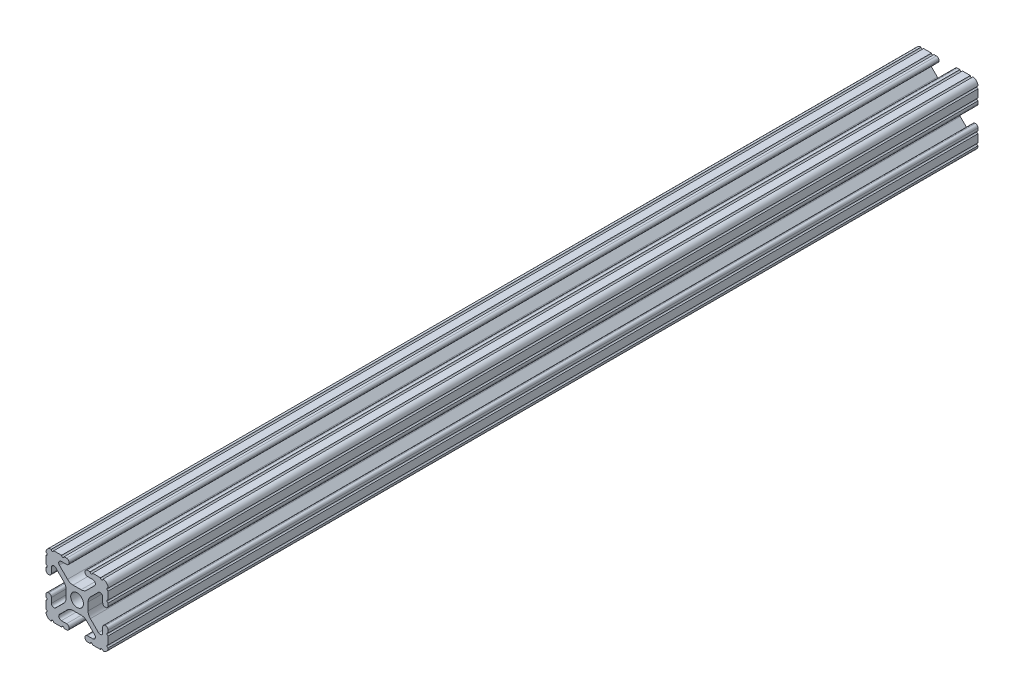
SolidWorks part; units mm, degrees
ref_plane "Front Plane" through (0, 0, 0) normal (0, 0, 1) x (1, 0, 0)
ref_plane "Top Plane" through (0, 0, 0) normal (0, 1, 0) x (1, 0, 0)
ref_plane "Right Plane" through (0, 0, 0) normal (1, 0, 0) x (0, 0, -1)
sketch "Sketch1" plane through (0, 0, 0) normal (0, 0, 1) x (1, 0, 0)
  line L88 (-7.1797, -8.6452) -> (-3.9523, -5.4237)
  line L89 (-1.7093, -4.4958) -> (1.7093, -4.4958)
  line L90 (3.9523, -5.4237) -> (7.1797, -8.6452)
  line L91 (6.4164, -10.4902) -> (4.2875, -10.4902)
  line L92 (3.2385, -11.5392) -> (3.2385, -11.651)
  line L93 (4.2875, -12.7) -> (5.3171, -12.7)
  line L94 (6.3331, -12.7) -> (9.5504, -12.7)
  line L95 (12.7, -9.5504) -> (12.7, -6.3331)
  line L96 (12.7, -5.3171) -> (12.7, -4.2875)
  line L97 (11.651, -3.2385) -> (11.5392, -3.2385)
  line L98 (10.4902, -4.2875) -> (10.4902, -6.4021)
  line L99 (8.7371, -7.1294) -> (5.441, -3.8408)
  line L100 (4.5085, -1.5932) -> (4.5085, 1.5932)
  line L101 (5.441, 3.8408) -> (8.7371, 7.1294)
  line L102 (10.4902, 6.4021) -> (10.4902, 4.2875)
  line L103 (11.5392, 3.2385) -> (11.651, 3.2385)
  line L104 (12.7, 4.2875) -> (12.7, 5.3171)
  line L105 (12.7, 6.3331) -> (12.7, 9.5504)
  line L106 (9.5504, 12.7) -> (6.3331, 12.7)
  line L107 (5.3171, 12.7) -> (4.2875, 12.7)
  line L108 (3.2385, 11.651) -> (3.2385, 11.5392)
  line L109 (4.2875, 10.4902) -> (6.4768, 10.4902)
  line L110 (7.207, 8.7244) -> (3.8983, 5.4232)
  line L111 (1.6558, 4.4958) -> (-1.6558, 4.4958)
  line L112 (-3.8983, 5.4232) -> (-7.207, 8.7244)
  line L113 (-6.4768, 10.4902) -> (-4.2875, 10.4902)
  line L114 (-3.2385, 11.5392) -> (-3.2385, 11.651)
  line L115 (-4.2875, 12.7) -> (-5.3171, 12.7)
  line L116 (-6.3331, 12.7) -> (-9.5504, 12.7)
  line L117 (-12.7, 9.5504) -> (-12.7, 6.3331)
  line L118 (-12.7, 5.3171) -> (-12.7, 4.2875)
  line L119 (-11.651, 3.2385) -> (-11.5392, 3.2385)
  line L120 (-10.4902, 4.2875) -> (-10.4902, 6.4021)
  line L121 (-8.7371, 7.1294) -> (-5.441, 3.8408)
  line L122 (-4.5085, 1.5932) -> (-4.5085, -1.5932)
  line L123 (-5.441, -3.8408) -> (-8.7371, -7.1294)
  line L124 (-10.4902, -6.4021) -> (-10.4902, -4.2875)
  line L125 (-11.5392, -3.2385) -> (-11.651, -3.2385)
  line L126 (-12.7, -4.2875) -> (-12.7, -5.3171)
  line L127 (-12.7, -6.3331) -> (-12.7, -9.5504)
  line L128 (-9.5504, -12.7) -> (-6.3331, -12.7)
  line L129 (-5.3171, -12.7) -> (-4.2875, -12.7)
  line L130 (-3.2385, -11.651) -> (-3.2385, -11.5392)
  line L131 (-4.2875, -10.4902) -> (-6.4164, -10.4902)
  circle A1 centre (0, 0) radius 2.6035
  arc A104 (-7.1797, -8.6452) -> (-6.4164, -10.4902) centre (-6.4164, -9.4098) ccw
  arc A105 (-1.7093, -4.4958) -> (-3.9523, -5.4237) centre (-1.7093, -7.6708) ccw
  arc A106 (3.9523, -5.4237) -> (1.7093, -4.4958) centre (1.7093, -7.6708) ccw
  arc A107 (6.4164, -10.4902) -> (7.1797, -8.6452) centre (6.4164, -9.4098) ccw
  arc A108 (4.2875, -10.4902) -> (3.2385, -11.5392) centre (4.2875, -11.5392) ccw
  arc A109 (3.2385, -11.651) -> (4.2875, -12.7) centre (4.2875, -11.651) ccw
  arc A110 (6.3331, -12.7) -> (5.3171, -12.7) centre (5.8251, -12.7) ccw
  arc A111 (10.5664, -12.6998) -> (9.5504, -12.7) centre (10.0584, -12.7) ccw
  arc A112 (10.5664, -12.6998) -> (12.6998, -10.5664) centre (10.5918, -10.5918) ccw
  arc A113 (12.7, -9.5504) -> (12.6998, -10.5664) centre (12.7, -10.0584) ccw
  arc A114 (12.7, -5.3171) -> (12.7, -6.3331) centre (12.7, -5.8251) ccw
  arc A115 (12.7, -4.2875) -> (11.651, -3.2385) centre (11.651, -4.2875) ccw
  arc A116 (11.5392, -3.2385) -> (10.4902, -4.2875) centre (11.5392, -4.2875) ccw
  arc A117 (8.7371, -7.1294) -> (10.4902, -6.4021) centre (9.4628, -6.4021) ccw
  arc A118 (4.5085, -1.5932) -> (5.441, -3.8408) centre (7.6835, -1.5932) ccw
  arc A119 (5.441, 3.8408) -> (4.5085, 1.5932) centre (7.6835, 1.5932) ccw
  arc A120 (10.4902, 6.4021) -> (8.7371, 7.1294) centre (9.4628, 6.4021) ccw
  arc A121 (10.4902, 4.2875) -> (11.5392, 3.2385) centre (11.5392, 4.2875) ccw
  arc A122 (11.651, 3.2385) -> (12.7, 4.2875) centre (11.651, 4.2875) ccw
  arc A123 (12.7, 6.3331) -> (12.7, 5.3171) centre (12.7, 5.8251) ccw
  arc A124 (12.6998, 10.5664) -> (12.7, 9.5504) centre (12.7, 10.0584) ccw
  arc A125 (12.6998, 10.5664) -> (10.5664, 12.6998) centre (10.5918, 10.5918) ccw
  arc A126 (9.5504, 12.7) -> (10.5664, 12.6998) centre (10.0584, 12.7) ccw
  arc A127 (5.3171, 12.7) -> (6.3331, 12.7) centre (5.8251, 12.7) ccw
  arc A128 (4.2875, 12.7) -> (3.2385, 11.651) centre (4.2875, 11.651) ccw
  arc A129 (3.2385, 11.5392) -> (4.2875, 10.4902) centre (4.2875, 11.5392) ccw
  arc A130 (7.207, 8.7244) -> (6.4768, 10.4902) centre (6.4768, 9.4563) ccw
  arc A131 (1.6558, 4.4958) -> (3.8983, 5.4232) centre (1.6558, 7.6708) ccw
  arc A132 (-3.8983, 5.4232) -> (-1.6558, 4.4958) centre (-1.6558, 7.6708) ccw
  arc A133 (-6.4768, 10.4902) -> (-7.207, 8.7244) centre (-6.4768, 9.4563) ccw
  arc A134 (-4.2875, 10.4902) -> (-3.2385, 11.5392) centre (-4.2875, 11.5392) ccw
  arc A135 (-3.2385, 11.651) -> (-4.2875, 12.7) centre (-4.2875, 11.651) ccw
  arc A136 (-6.3331, 12.7) -> (-5.3171, 12.7) centre (-5.8251, 12.7) ccw
  arc A137 (-10.5664, 12.6998) -> (-9.5504, 12.7) centre (-10.0584, 12.7) ccw
  arc A138 (-10.5664, 12.6998) -> (-12.6998, 10.5664) centre (-10.5918, 10.5918) ccw
  arc A139 (-12.7, 9.5504) -> (-12.6998, 10.5664) centre (-12.7, 10.0584) ccw
  arc A140 (-12.7, 5.3171) -> (-12.7, 6.3331) centre (-12.7, 5.8251) ccw
  arc A141 (-12.7, 4.2875) -> (-11.651, 3.2385) centre (-11.651, 4.2875) ccw
  arc A142 (-11.5392, 3.2385) -> (-10.4902, 4.2875) centre (-11.5392, 4.2875) ccw
  arc A143 (-8.7371, 7.1294) -> (-10.4902, 6.4021) centre (-9.4628, 6.4021) ccw
  arc A144 (-4.5085, 1.5932) -> (-5.441, 3.8408) centre (-7.6835, 1.5932) ccw
  arc A145 (-5.441, -3.8408) -> (-4.5085, -1.5932) centre (-7.6835, -1.5932) ccw
  arc A146 (-10.4902, -6.4021) -> (-8.7371, -7.1294) centre (-9.4628, -6.4021) ccw
  arc A147 (-10.4902, -4.2875) -> (-11.5392, -3.2385) centre (-11.5392, -4.2875) ccw
  arc A148 (-11.651, -3.2385) -> (-12.7, -4.2875) centre (-11.651, -4.2875) ccw
  arc A149 (-12.7, -6.3331) -> (-12.7, -5.3171) centre (-12.7, -5.8251) ccw
  arc A150 (-12.6998, -10.5664) -> (-12.7, -9.5504) centre (-12.7, -10.0584) ccw
  arc A151 (-12.6998, -10.5664) -> (-10.5664, -12.6998) centre (-10.5918, -10.5918) ccw
  arc A152 (-9.5504, -12.7) -> (-10.5664, -12.6998) centre (-10.0584, -12.7) ccw
  arc A153 (-5.3171, -12.7) -> (-6.3331, -12.7) centre (-5.8251, -12.7) ccw
  arc A154 (-4.2875, -12.7) -> (-3.2385, -11.651) centre (-4.2875, -11.651) ccw
  arc A155 (-3.2385, -11.5392) -> (-4.2875, -10.4902) centre (-4.2875, -11.5392) ccw
extrude "Boss-Extrude1" add sketch "Sketch1" along normal mid plane 355.6
